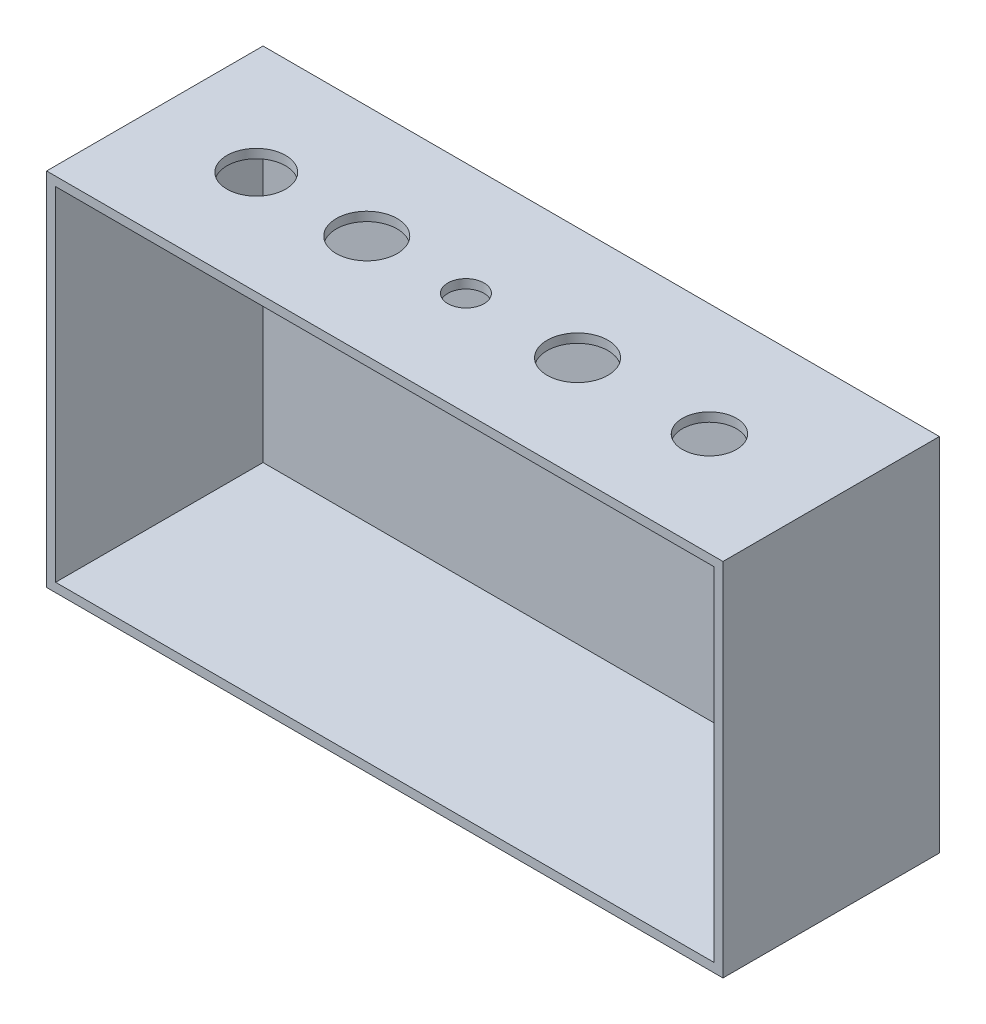
SolidWorks part; units mm, degrees
material "ABS PC"
ref_plane "Front Plane" through (0, 0, 0) normal (0, 0, 1) x (1, 0, 0)
ref_plane "Top Plane" through (0, 0, 0) normal (0, 1, 0) x (1, 0, 0)
ref_plane "Right Plane" through (0, 0, 0) normal (1, 0, 0) x (0, 0, -1)
sketch "Sketch1" plane through (0, 0, 0) normal (0, 1, 0) x (1, 0, 0)
  line L1 (0, 50) -> (150, 50)
  line L2 (0, 50) -> (0, 0)
  line L3 (0, 0) -> (150, 0)
  line L4 (150, 50) -> (150, 0)
  dimension "D1" = 50
  dimension "D2" = 150
extrude "Extrude5" add sketch "Sketch1" against normal blind 80
shell "Shell1" thickness 2
sketch "Sketch8" plane through (0, 0, 0) normal (0, 1, 0) x (1, 0, 0)
  line L0 (0, 25) -> (150, 25) construction
  line L1 (0, 50) -> (0, 0) construction
  line L2 (150, 50) -> (150, 0) construction
  line L3 (23.5, 50) -> (23.5, 0) construction
  line L4 (0, 50) -> (150, 50) construction
  line L5 (0, 0) -> (150, 0) construction
  line L6 (48, 50) -> (48, 0) construction
  line L7 (70, 50) -> (70, 0) construction
  line L8 (94.75, 50) -> (94.75, 0) construction
  line L9 (124, 50) -> (124, 0) construction
  line L10 (75, 50) -> (75, 0) construction
  circle A0 centre (23.5, 25) radius 6.5
  circle A1 centre (48, 25) radius 6.75
  circle A2 centre (70, 25) radius 4
  circle A3 centre (94.75, 25) radius 6.75
  circle A4 centre (124, 25) radius 6
  point P20 (23.5, 25)
  point P21 (48, 25)
  point P22 (70, 25)
  point P23 (94.75, 25)
  point P24 (124, 25)
  dimension "D7" = 13
  dimension "D8" = 13.5
  dimension "D9" = 8
  dimension "D10" = 13.5
  dimension "D11" = 12
  dimension "D1" = 23.5
  dimension "D2" = 24.5
  dimension "D3" = 22
  dimension "D4" = 24.75
  dimension "D5" = 29.25
  dimension "D6" = 26
extrude "Extrude6" cut sketch "Sketch8" against normal up to next
sketch "Sketch9" plane through (0, 0, 0) normal (0, 0, 1) x (1, 0, 0)
  line L0 (0, -40) -> (150, -40) construction
  line L1 (0, -80) -> (0, 0) construction
  line L2 (150, -80) -> (150, 0) construction
sketch "Sketch10" plane through (0, 0, 0) normal (1, 0, 0) x (0, 0, -1)
  line L0 (0, -40) -> (50, -40) construction
  line L1 (0, -80) -> (0, 0) construction
  line L2 (50, -80) -> (50, 0) construction
  line L5 (48, -35) -> (50, -35)
  line L6 (48, -35) -> (48, -45)
  line L7 (48, -45) -> (50, -45)
  line L8 (50, -35) -> (50, -45)
  point P10 (50, -40)
  dimension "D1" = 10
  dimension "D2" = 2
sketch "Sketch11" plane through (0, 0, 0) normal (0, 1, 0) x (1, 0, 0)
  line L0 (75, 0) -> (75, 50) construction
  line L1 (0, 0) -> (150, 0) construction
  line L2 (0, 50) -> (150, 50) construction
  line L3 (0, 25) -> (150, 25) construction
  line L4 (0, 50) -> (0, 0) construction
  line L5 (150, 50) -> (150, 0) construction
ref_point "Point1"
ref_point "Point2"
ref_plane "Plane1" through (75, 0, 0) normal (-1, 0, 0) x (0, 0, 1)
sketch "Sketch12" plane through (0, 0, 0) normal (-1, 0, 0) x (0, 0, 1)
  line L0 (-50, -80) -> (0, -80) construction
  line L1 (0, 0) -> (-2, 0)
  line L2 (0, 0) -> (0, -80)
  line L3 (0, -80) -> (-2, -80)
  line L4 (-2, 0) -> (-2, -80)
extrude "Cut-Extrude1" cut sketch "Sketch12" against normal blind 200
